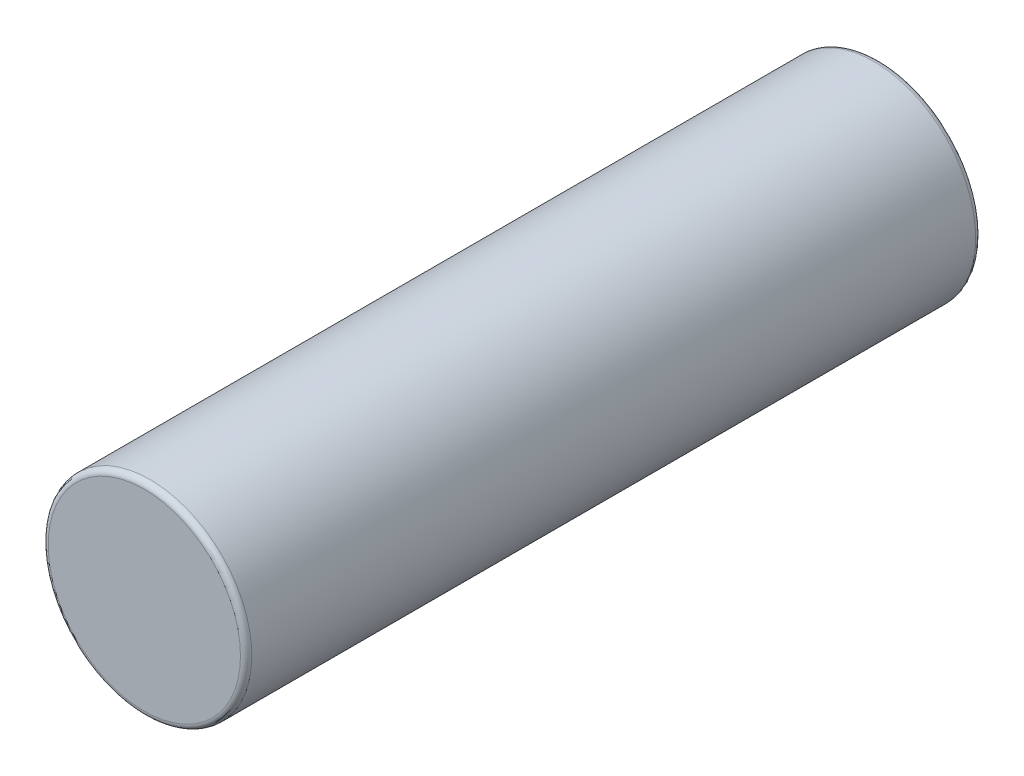
SolidWorks part; units mm, degrees
ref_plane "Спереди" through (0, 0, 0) normal (0, 0, 1) x (1, 0, 0)
ref_plane "Сверху" through (0, 0, 0) normal (0, 1, 0) x (1, 0, 0)
ref_plane "Справа" through (0, 0, 0) normal (1, 0, 0) x (0, 0, -1)
sketch "Эскиз1" plane through (0, 0, 0) normal (0, 0, 1) x (1, 0, 0)
  circle A0 centre (0, 0) radius 9
  dimension "D1" = 18
extrude "Бобышка-Вытянуть1" add sketch "Эскиз1" along normal blind 65
fillet "Скругление1" radius 0.5 2 edges at (9, 0, 65) (9, 0, 0)
